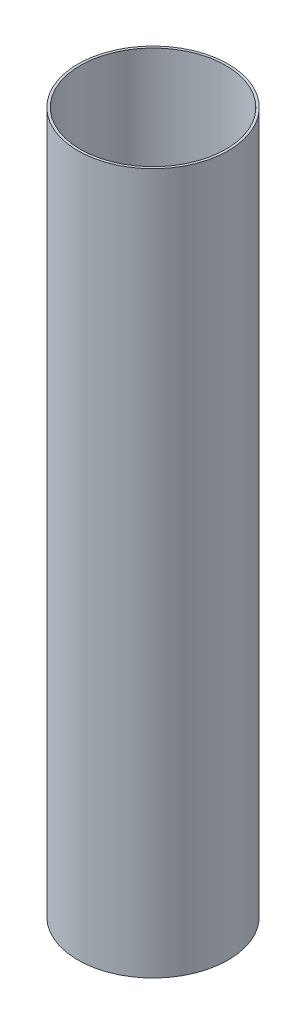
SolidWorks part; units mm, degrees
material "6061-T6 (SS)"
ref_plane "Front Plane" through (0, 0, 0) normal (0, 0, 1) x (1, 0, 0)
ref_plane "Top Plane" through (0, 0, 0) normal (0, 1, 0) x (1, 0, 0)
ref_plane "Right Plane" through (0, 0, 0) normal (1, 0, 0) x (0, 0, -1)
sketch "Sketch1" plane through (0, 0, 0) normal (0, 1, 0) x (1, 0, 0)
  circle A0 centre (0, 0) radius 98.425
  dimension "D1" = 196.85
extrude "Extrude-Thin1" add sketch "Sketch1" along normal blind 948.69 thin
